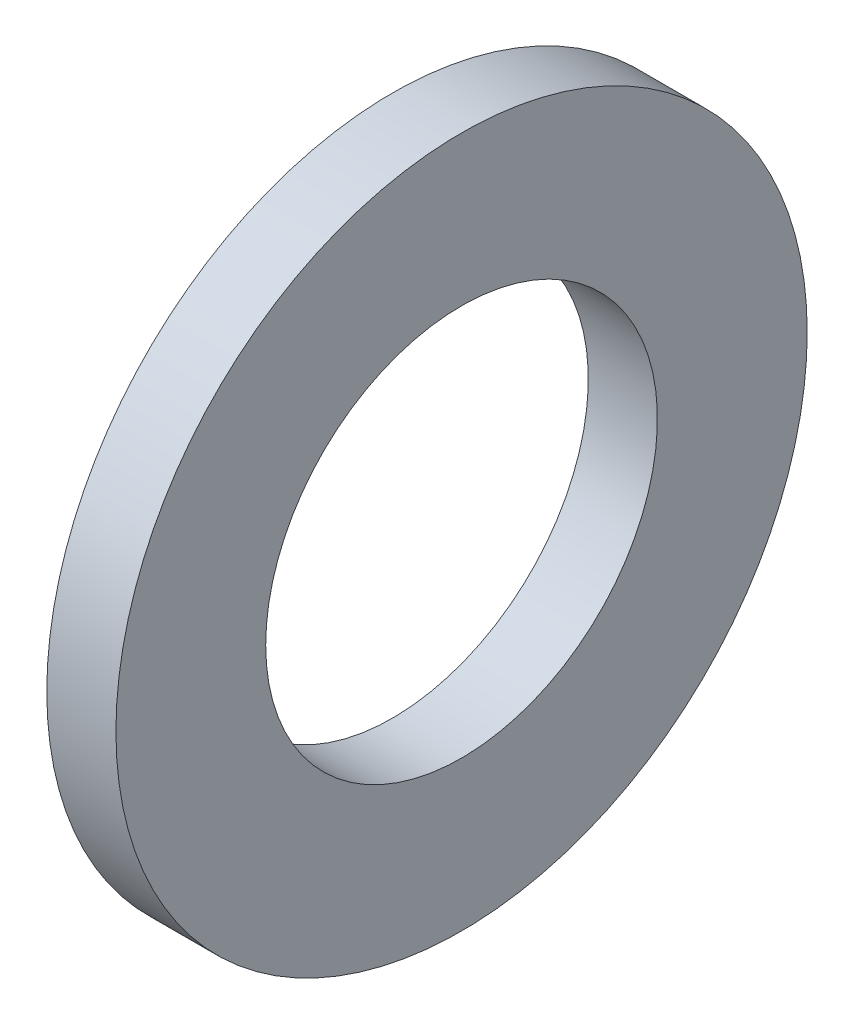
SolidWorks part; units mm, degrees
ref_plane "Plane1" through (0, 0, 0) normal (0, 0, 1) x (1, 0, 0)
ref_plane "Plane2" through (0, 0, 0) normal (0, 1, 0) x (1, 0, 0)
ref_plane "Plane3" through (0, 0, 0) normal (1, 0, 0) x (0, 0, -1)
sketch "Sketch1" plane through (0, 0, 0) normal (0, 0, 1) x (1, 0, 0)
  line L0 (-34.925, 0) -> (9.525, 0) construction
  line L1 (0, 8.5) -> (0, 15)
  line L2 (0, 15) -> (-3, 15)
  line L3 (-3, 15) -> (-3, 8.5)
  line L4 (-3, 8.5) -> (0, 8.5)
  dimension "Thickness" = 3
  dimension "Inside_dia" = 17
  dimension "Outside_dia" = 30
revolve "Base-Revolve" add sketch "Sketch1" angle 360 about L0
